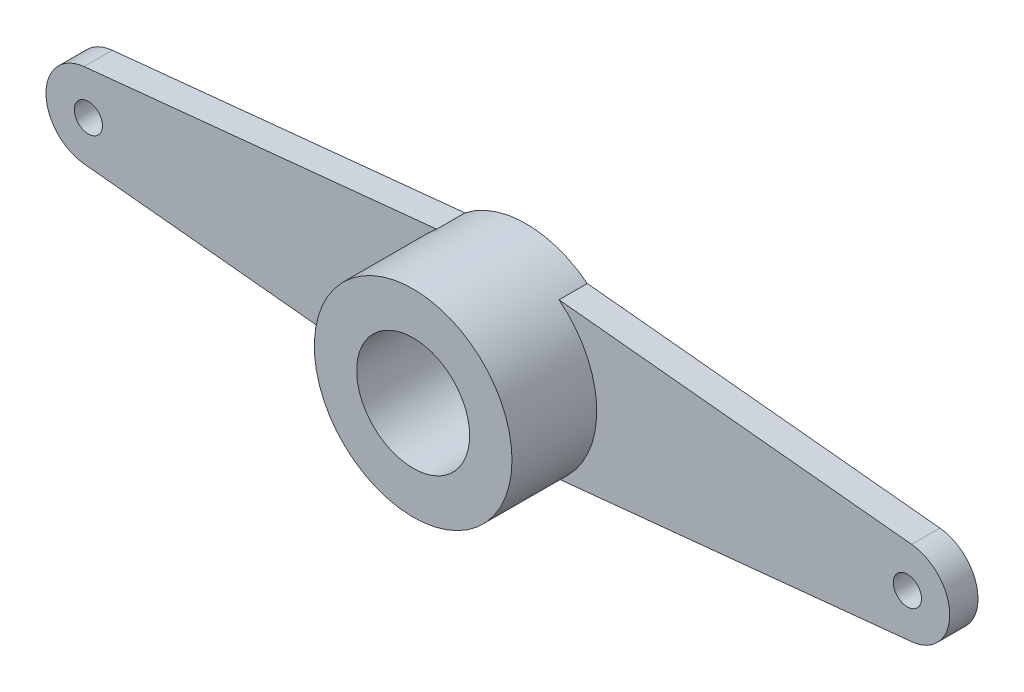
SolidWorks part; units mm, degrees
ref_plane "前视基准面" through (0, 0, 0) normal (0, 0, 1) x (1, 0, 0)
ref_plane "上视基准面" through (0, 0, 0) normal (0, 1, 0) x (1, 0, 0)
ref_plane "右视基准面" through (0, 0, 0) normal (1, 0, 0) x (0, 0, -1)
sketch "草图1" plane through (0, 0, 0) normal (0, 0, 1) x (1, 0, 0)
  line L0 (0, 0) -> (14.5, 0) construction
  line L1 (2.1651, 2.75) -> (14.6503, 1.4924)
  line L2 (2.1651, -2.75) -> (14.6503, -1.4924)
  circle A0 centre (14.5, 0) radius 1.5
  circle A1 centre (0, 0) radius 3.5
  circle A2 centre (0, 0) radius 2
  circle A3 centre (14.5, 0) radius 0.5
  dimension "D2" = 3
  dimension "D3" = 7
  dimension "D4" = 4
  dimension "D6" = 1
  dimension "D1" = 14.5
  dimension "D5" = 2.75
extrude "凸台-拉伸2" add sketch "草图1" along normal blind 1
sketch "草图2" plane through (0, 0, 1) normal (0, 0, 1) x (1, 0, 0)
  circle A0 centre (0, 0) radius 2
  circle A1 centre (0, 0) radius 3.5
  circle A2 centre (0, 0) radius 2 construction
  arc A3 (2.1651, 2.75) -> (2.1651, -2.75) centre (0, 0) ccw construction
extrude "凸台-拉伸3" add sketch "草图2" along normal blind 3
mirror "镜向1" about plane through (0, 0, 0) normal (1, 0, 0) of "凸台-拉伸2"
